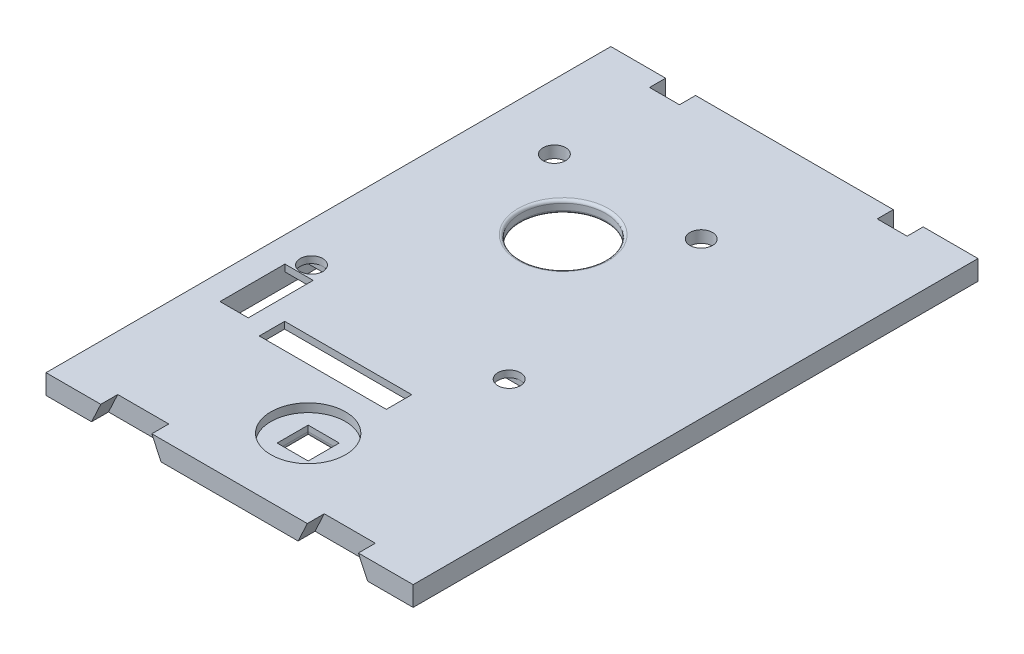
SolidWorks part; units mm, degrees
ref_plane "Front Plane" through (0, 0, 0) normal (0, 0, 1) x (1, 0, 0)
ref_plane "Top Plane" through (0, 0, 0) normal (0, 1, 0) x (1, 0, 0)
ref_plane "Right Plane" through (0, 0, 0) normal (1, 0, 0) x (0, 0, -1)
sketch "Sketch1" plane through (0, 0, 0) normal (0, 1, 0) x (1, 0, 0)
  line L1 (-32.5, -50) -> (32.5, -50)
  line L2 (-32.5, -50) -> (-32.5, 50)
  line L3 (-32.5, 50) -> (32.5, 50)
  line L4 (32.5, -50) -> (32.5, 50)
  line L5 (-32.5, -50) -> (32.5, 50) construction
  line L6 (-32.5, 50) -> (32.5, -50) construction
  point P0 (0, 0)
  dimension "D1" = 65
  dimension "D2" = 100
extrude "Boss-Extrude1" add sketch "Sketch1" along normal blind 3.5
sketch "Sketch2" plane through (0, 0, 0) normal (0, 1, 0) x (1, 0, 0)
  line L0 (-32.5, -50) -> (32.5, -50) construction
  line L1 (-28, -25.5) -> (12, -25.5)
  line L2 (-28, -25.5) -> (-28, 35.5)
  line L3 (-28, 35.5) -> (12, 35.5)
  line L4 (12, -25.5) -> (12, 35.5)
  line L5 (-28, -25.5) -> (12, 35.5) construction
  line L6 (-28, 35.5) -> (12, -25.5) construction
  line L7 (-32.5, 50) -> (-32.5, -50) construction
  point P0 (-8, 5)
  dimension "D1" = 61
  dimension "D2" = 40
  dimension "D3" = 55
  dimension "D4" = 24.5
extrude "Cut-Extrude1" cut sketch "Sketch2" along normal blind 1.4 contours L1 L4 L3 L2
sketch "Sketch3" plane through (0, 0, 0) normal (0, 1, 0) x (1, 0, 0)
  line L1 (-28, 35.5) -> (-21, 35.5)
  line L2 (-28, 35.5) -> (-28, 28.5)
  line L3 (-28, 28.5) -> (-21, 28.5)
  line L4 (-21, 35.5) -> (-21, 28.5)
  circle A0 centre (-21, 28.5) radius 2
  dimension "D1" = 7
  dimension "D2" = 7
sketch "Sketch4" plane through (0, 0, 0) normal (0, 1, 0) x (1, 0, 0)
  line L1 (12, 35.5) -> (5, 35.5)
  line L2 (12, 35.5) -> (12, 28.5)
  line L3 (12, 28.5) -> (5, 28.5)
  line L4 (5, 35.5) -> (5, 28.5)
  circle A0 centre (5, 28.5) radius 2
  dimension "D1" = 7
  dimension "D2" = 7
extrude "Cut-Extrude3" cut sketch "Sketch3" along normal blind 3.5 contours A0
extrude "Cut-Extrude5" cut sketch "Sketch4" along normal blind 3.5 contours A0
sketch "Sketch6" plane through (0, 0, 0) normal (0, 1, 0) x (1, 0, 0)
  line L1 (-28, -25.5) -> (-25.5, -25.5)
  line L2 (-28, -25.5) -> (-28, -10)
  line L3 (-28, -10) -> (-25.5, -10)
  line L4 (-25.5, -25.5) -> (-25.5, -10)
  circle A0 centre (-25.5, -10) radius 2
  dimension "D1" = 15.5
  dimension "D2" = 2.5
extrude "Cut-Extrude6" cut sketch "Sketch6" along normal blind 3.5 contours A0
sketch "Sketch7" plane through (0, 0, 0) normal (0, 1, 0) x (1, 0, 0)
  line L1 (12, -25.5) -> (9.5, -25.5)
  line L2 (12, -25.5) -> (12, -10)
  line L3 (12, -10) -> (9.5, -10)
  line L4 (9.5, -25.5) -> (9.5, -10)
  circle A0 centre (9.5, -10) radius 2
  dimension "D1" = 2.5
  dimension "D2" = 15.5
extrude "Cut-Extrude7" cut sketch "Sketch7" along normal blind 3.5 contours A0
sketch "Sketch8" plane through (0, 0, 0) normal (0, 1, 0) x (1, 0, 0)
  line L0 (-28, -25.5) -> (-28, 35.5) construction
  line L1 (-28, -23.7) -> (-23, -23.7)
  line L2 (-28, -23.7) -> (-28, -12.2)
  line L3 (-28, -12.2) -> (-23, -12.2)
  line L4 (-23, -23.7) -> (-23, -12.2)
  dimension "D1" = 1.8
  dimension "D2" = 11.5
  dimension "D3" = 5
sketch "Sketch9" plane through (0, 0, 0) normal (0, 1, 0) x (1, 0, 0)
  line L0 (-28, -25.5) -> (12, -25.5) construction
  line L1 (-17.5, -3.5) -> (1.5, -3.5)
  line L2 (-17.5, -3.5) -> (-17.5, 2.5)
  line L3 (-17.5, 2.5) -> (1.5, 2.5)
  line L4 (1.5, -3.5) -> (1.5, 2.5)
  line L5 (-17.5, -3.5) -> (1.5, 2.5) construction
  line L6 (-17.5, 2.5) -> (1.5, -3.5) construction
  point P0 (-8, -0.5)
  point P8 (-8, -25.5)
  dimension "D1" = 25
  dimension "D2" = 19
  dimension "D3" = 6
extrude "Cut-Extrude9" cut sketch "Sketch9" along normal blind 2.3
sketch "Sketch10" plane through (0, 0, 0) normal (0, 1, 0) x (1, 0, 0)
  line L0 (-28, -25.5) -> (12, -25.5) construction
  line L1 (-19.25, -25.5) -> (3.25, -25.5)
  line L2 (-19.25, -25.5) -> (-19.25, -21)
  line L3 (-19.25, -21) -> (3.25, -21)
  line L4 (3.25, -25.5) -> (3.25, -21)
  line L5 (-19.25, -25.5) -> (3.25, -21) construction
  line L6 (-19.25, -21) -> (3.25, -25.5) construction
  point P0 (-8, -23.25)
  point P5 (-8, -25.5)
  point P8 (-8, -25.5)
  dimension "D1" = 22.5
  dimension "D2" = 4.5
extrude "Cut-Extrude10" cut sketch "Sketch10" along normal blind 3.5
sketch "Sketch11" plane through (0, 0, 0) normal (0, 1, 0) x (1, 0, 0)
  line L0 (12, -25.5) -> (12, 35.5) construction
  line L1 (-28, -25.5) -> (3.25, -25.5)
  line L2 (-28, -25.5) -> (-28, -8)
  line L3 (-28, -8) -> (12, -8)
  line L4 (12, -21) -> (12, -8)
  line L7 (12, -21) -> (12, -25.5)
  line L8 (12, -25.5) -> (3.25, -25.5)
extrude "Cut-Extrude11" cut sketch "Sketch11" along normal blind 2.3
sketch "Sketch12" plane through (0, 0, 0) normal (0, 1, 0) x (1, 0, 0)
  line L1 (28, -20.8) -> (28, 25)
  line L2 (12, -25.5) -> (12, -20.8)
  line L3 (12, -25.5) -> (12, 35.5) construction
  line L4 (12, -20.8) -> (28, -20.8)
  line L6 (28, 25) -> (30.7, 25)
  line L9 (30.7, 25) -> (30.7, -25.5)
  line L10 (30.7, -25.5) -> (12, -25.5)
  dimension "D1" = 2.7
  dimension "D2" = 4.7
  dimension "D3" = 16
  dimension "D4" = 50.5
extrude "Cut-Extrude15" cut sketch "Sketch12" along normal blind 2.5
sketch "Sketch18" plane through (0, 0, 0) normal (0, 1, 0) x (1, 0, 0)
  line L0 (-28, -8) -> (-28, 35.5) construction
  line L1 (-28.8, -25.5) -> (-31.5, -25.5)
  line L2 (-28.8, -25.5) -> (-28.8, 25)
  line L3 (-28.8, 25) -> (-31.5, 25)
  line L4 (-31.5, -25.5) -> (-31.5, 25)
  line L5 (30.7, 25) -> (-31.5, 25) construction
  line L6 (-28, -25.5) -> (-31.5, -25.5) construction
  dimension "D1" = 0.8
  dimension "D2" = 2.7
  dimension "D3" = 50.5
extrude "Cut-Extrude18" cut sketch "Sketch18" along normal blind 2.5
extrude "Cut-Extrude25" cut sketch "Sketch8" along normal blind 3.5 contours L1 L4 L3 L2
sketch "Sketch20" plane through (0, 1.4, 0) normal (0, -1, 0) x (1, 0, 0)
  circle A0 centre (-7.8879, -16.952) radius 7.5
  dimension "D1" = 15
extrude "Cut-Extrude27" cut sketch "Sketch20" against normal through all both and the other way through all
sketch "Sketch21" plane through (0, 0, 0) normal (0, -1, 0) x (1, 0, 0)
  line L0 (32.5, -50) -> (-32.5, -50) construction
  line L1 (-22.8, -50) -> (-17.5, -50)
  line L2 (-22.8, -50) -> (-22.8, -47.15)
  line L3 (-22.8, -47.15) -> (-17.5, -47.15)
  line L4 (-17.5, -50) -> (-17.5, -47.15)
  line L5 (0, 0) -> (0, -11.0705) construction
  line L7 (17.5, -50) -> (17.5, -47.15)
  line L8 (22.8, -47.15) -> (17.5, -47.15)
  line L9 (22.8, -50) -> (22.8, -47.15)
  line L10 (22.8, -50) -> (17.5, -50)
  dimension "D1" = 9.7
  dimension "D2" = 5.3
  dimension "D3" = 2.85
  dimension "D4" = 90
  dimension "D5" = 9.7
  dimension "D6" = 5.3
  dimension "D7" = 2.85
extrude "Cut-Extrude28" cut sketch "Sketch21" against normal blind 3.5
sketch "Sketch25" plane through (0, 0, 50) normal (0, 0, 1) x (1, 0, 0)
  line L0 (-32.5, 3.5) -> (-22.8, 3.5) construction
  line L1 (-32.5, 3.5) -> (32.5, 3.5) construction
  line L2 (-22.8, 3.5) -> (-27.4678, -6.5102) construction
  line L3 (-22.8, 3.5) -> (-24.4321, 0)
  line L4 (-32.5, 0) -> (32.5, 0) construction
  line L5 (-24.4321, 0) -> (-12.1321, 0)
  line L6 (-12.1321, 0) -> (-14.524, 5.1296) construction
  line L7 (-12.1321, 0) -> (-13.7642, 3.5)
  line L8 (-13.7642, 3.5) -> (-22.8, 3.5)
  line L9 (0, 0) -> (0, 8.3366) construction
  line L12 (13.7642, 3.5) -> (22.8, 3.5)
  line L13 (12.1321, 0) -> (13.7642, 3.5)
  line L14 (24.4321, 0) -> (12.1321, 0)
  line L15 (22.8, 3.5) -> (24.4321, 0)
  point P17 (32.5, 3.5)
  line M8 (-32.5, 0) -> (32.5, 0)
  line M10 (32.5, 3.5) -> (-32.5, 3.5)
  dimension "D1" = 9.7
  dimension "D2" = 65
  dimension "D3" = 12.3
  dimension "D4" = 65
  dimension "D5" = 9.7
  dimension "D6" = 12.3
  dimension "D7" = 24.2642
extrude "Cut-Extrude30" cut sketch "Sketch25" against normal blind 3 contours L15 L13 M10 M8 | L3 L5 L7 L8
fillet "Fillet2" radius 0.5 2 edges at (-7.8879, 3.5, -24.452) (-7.8879, 1.4, -24.452)
sketch "Sketch27" plane through (0, 3.5, 0) normal (0, 1, 0) x (1, 0, 0)
  circle A0 centre (0, -36.0835) radius 6.6
  dimension "D1" = 13.2
extrude "Cut-Extrude32" cut sketch "Sketch27" against normal blind 1.5 contours A0
sketch "Sketch28" plane through (0, 2, 0) normal (0, 1, 0) x (1, 0, 0)
  line L1 (-2.75, -33.3335) -> (2.75, -33.3335)
  line L2 (-2.75, -33.3335) -> (-2.75, -38.8335)
  line L3 (-2.75, -38.8335) -> (2.75, -38.8335)
  line L4 (2.75, -33.3335) -> (2.75, -38.8335)
  line L5 (-2.75, -33.3335) -> (2.75, -38.8335) construction
  line L6 (-2.75, -38.8335) -> (2.75, -33.3335) construction
  point P0 (0, -36.0835)
  dimension "D1" = 5.5
  dimension "D2" = 5.5
extrude "Cut-Extrude33" cut sketch "Sketch28" against normal through all
fillet "Fillet4" radius 1 4 edges at (-2.75, 0, 36.0835) (0, 0, 38.8335) (2.75, 0, 36.0835) (0, 0, 33.3335)
